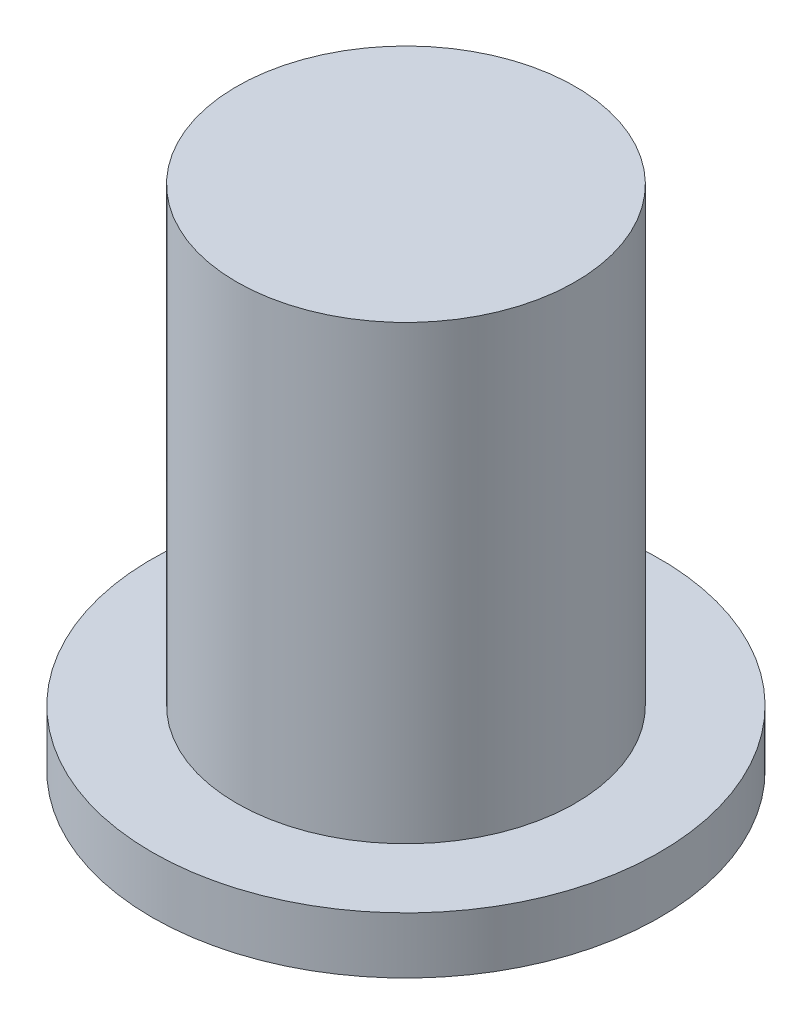
SolidWorks part; units mm, degrees
ref_plane "Front Plane" through (0, 0, 0) normal (0, 0, 1) x (1, 0, 0)
ref_plane "Top Plane" through (0, 0, 0) normal (0, 1, 0) x (1, 0, 0)
ref_plane "Right Plane" through (0, 0, 0) normal (1, 0, 0) x (0, 0, -1)
sketch "Sketch1" plane through (0, 0, 0) normal (0, 1, 0) x (1, 0, 0)
  circle A0 centre (0, 0) radius 4.5
  dimension "D1" = 9
extrude "Boss-Extrude1" add sketch "Sketch1" along normal blind 1 contours A0
sketch "Sketch2" plane through (0, 1, 0) normal (0, 1, 0) x (1, 0, 0)
  circle A0 centre (0, 0) radius 3
  dimension "D1" = 6
extrude "Boss-Extrude2" add sketch "Sketch2" along normal blind 8
